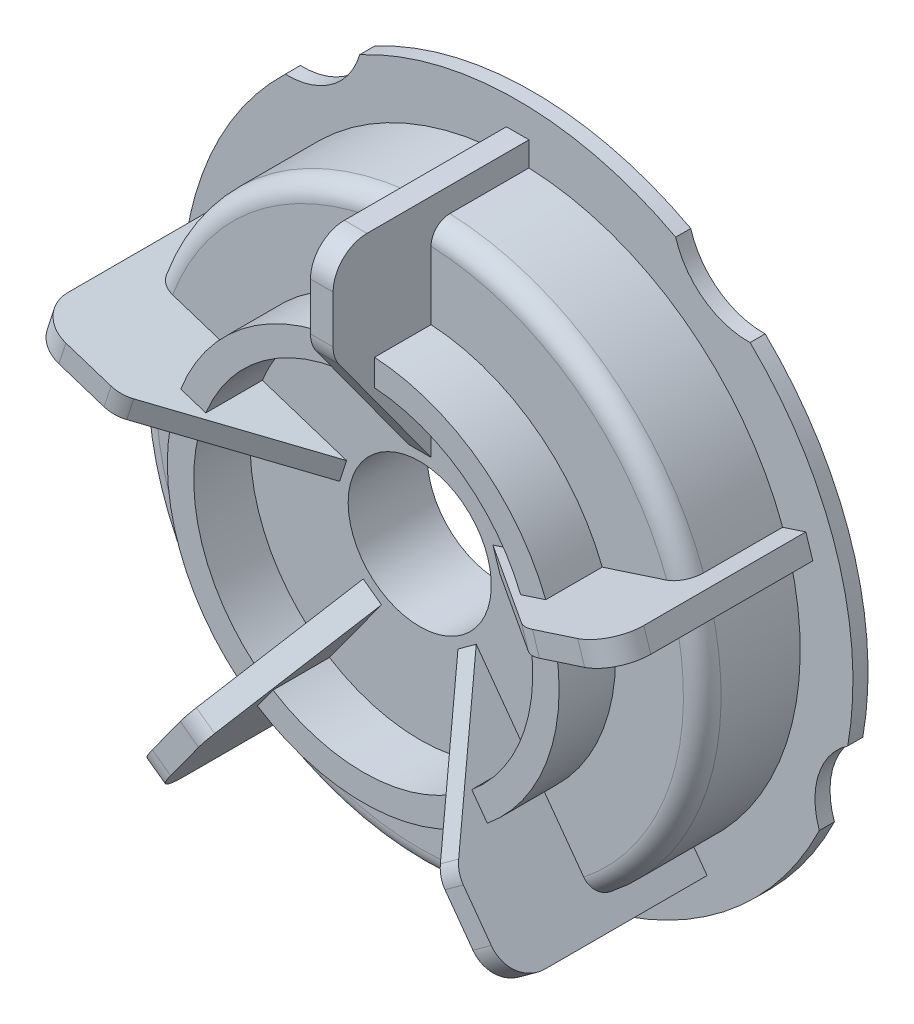
SolidWorks part; units mm, degrees
material "Melamine resin"
ref_plane "Front Plane" through (0, 0, 0) normal (0, 0, 1) x (1, 0, 0)
ref_plane "Top Plane" through (0, 0, 0) normal (0, 1, 0) x (1, 0, 0)
ref_plane "Right Plane" through (0, 0, 0) normal (1, 0, 0) x (0, 0, -1)
sketch "Sketch2" plane through (0, 0, 0) normal (1, 0, 0) x (0, 0, -1)
  line L0 (2.5, 44.5) -> (2.5, 37.5)
  line L1 (2.5, 37.5) -> (-10.5, 37.5)
  line L2 (-10.5, 37.5) -> (-10.5, 26)
  line L3 (-10.5, 9.5) -> (0, 9.5)
  line L4 (45.4382, 0) -> (-35.8369, 0) construction
  line L5 (4.5, 44.5) -> (4.5, 35.5)
  line L6 (4.5, 35.5) -> (-8.5, 35.5)
  line L7 (-8.5, 35.5) -> (-8.5, 11.5)
  line L8 (-8.5, 11.5) -> (0, 11.5)
  line L9 (2.5, 44.5) -> (4.5, 44.5)
  line L10 (0, 9.5) -> (0, 11.5)
  line L11 (-10.5, 22.5) -> (-18, 22.5)
  line L12 (-18, 22.5) -> (-18, 26)
  line L13 (-18, 26) -> (-10.5, 26)
  line L14 (-10.5, 22.5) -> (-10.5, 9.5)
  line L15 (-10.5, 37.5) -> (-10.5, 9.5) construction
  dimension "D2" = 89
  dimension "D3" = 19
  dimension "D4" = 75
  dimension "D7" = 3.5
  dimension "D8" = 7.5
  dimension "D9" = 52
  dimension "D1" = 15
  dimension "D5" = 4.5
  dimension "D6" = 2
revolve "Revolve1" add sketch "Sketch2" angle 360 about L4
fillet "Fillet1" radius 2.5 1 edges at (-37.5, 0, 10.5)
sketch "Sketch3" plane through (0, 0, 0) normal (1, 0, 0) x (0, 0, -1)
  line L0 (2.5, 40.7) -> (-19, 40.7)
  line L1 (2.5, 44.5) -> (2.5, -44.5) construction
  line L2 (-23.5, 36.2) -> (-23.5, 28.593)
  line L3 (-10.5, 10.7) -> (-23.5, 28.593)
  line L4 (-10.5, 35) -> (-10.5, -35) construction
  line L5 (4.5, -44.5) -> (4.5, 44.5) construction
  line L6 (-10.5, 22.5) -> (-10.5, -22.5) construction
  line L7 (0, -9.5) -> (0, 9.5) construction
  line L8 (0, -9.5) -> (0, 9.5) construction
  line L9 (0, 9.5) -> (-30.465, 9.5) construction
  line L10 (-10.5, 10.7) -> (-10.5, 33.4608)
  line L11 (-10.5, 33.4608) -> (-6.9188, 36.95)
  line L12 (-6.9188, 36.95) -> (2.5, 36.95)
  line L13 (2.5, 37.5) -> (2.5, -37.5) construction
  line L14 (2.5, 36.95) -> (2.5, 40.7)
  arc A0 (-19, 40.7) -> (-23.5, 36.2) centre (-19, 36.2) ccw
  point P19 (0, 0)
  dimension "D1" = 4.5
  dimension "D2" = 28
  dimension "D3" = 36
  dimension "D4" = 19
  dimension "D5" = 31.2
  dimension "D6" = 1.2
  dimension "D7" = 5
  dimension "D8" = 9.4188
  dimension "D9" = 3.75
extrude "Boss-Extrude1" add sketch "Sketch3" along normal mid plane 3
fillet "Fillet2" radius 4 1 edges at (0, 28.593, 23.5)
pattern_circular "CirPattern1" count 5 over 360 about axis through (0, 0, 0) along (0, 0, 1) of "Boss-Extrude1", "Fillet2"
sketch "Sketch4" plane through (0, 0, -4.5) normal (0, 0, -1) x (-1, 0, 0)
  circle A0 centre (0, -52) radius 10
  circle A1 centre (0, 0) radius 44.5 construction
  point P2 (0, -44.5)
  point P4 (0, -42)
  dimension "D1" = 20
  dimension "D2" = 2.5
extrude "Cut-Extrude1" cut sketch "Sketch4" against normal through all and the other way through all
sketch "Sketch5" plane through (0, 0, 8.5) normal (0, 0, -1) x (-1, 0, 0)
  line L1 (-2.9973, -35.3732) -> (0, -37.1037)
  line L2 (0, -37.1037) -> (2.9973, -35.3732)
  arc A0 (-2.9973, -35.3732) -> (2.9973, -35.3732) centre (0, -35.5) cw
  circle A1 centre (0, 0) radius 35.5 construction
  arc A2 (-19.6342, -29.5761) -> (19.6342, -29.5761) centre (0, 0) ccw construction
  dimension "D1" = 3
  dimension "D2" = 120
extrude "Boss-Extrude2" add sketch "Sketch5" along normal offset from surface (12 mm away) 1 up to face at (0, 1.25, -4.5)
sketch "Sketch6" plane through (0, 0, 8.5) normal (0, 0, -1) x (-1, 0, 0)
  line L1 (0.875, -34.75) -> (-0.875, -34.75)
  line L2 (0.875, -34.75) -> (0.875, -10.75)
  line L3 (0.875, -10.75) -> (-0.875, -10.75)
  line L4 (-0.875, -34.75) -> (-0.875, -10.75)
  point P4 (0, -34.75)
  dimension "D1" = 1.75
  dimension "D2" = 24
  dimension "D3" = 10.75
extrude "Boss-Extrude3" add sketch "Sketch6" along normal up to surface (8.5 mm away) up to face at (-11.5, 0, 0)
pattern_circular "CirPattern2" count 5 over 360 about axis through (0, 0, 0) along (0, 0, 1) of "Boss-Extrude2", "Boss-Extrude3", "Cut-Extrude1"
equation "\"A\"= 89"
equation "\"B\"= 15"
equation "\"C\"= 3.5"
equation "\"D2@Sketch2\"=\"A\""
equation "\"D7@Sketch2\"=\"C\""
equation "\"D1@Sketch2\"=\"B\""
